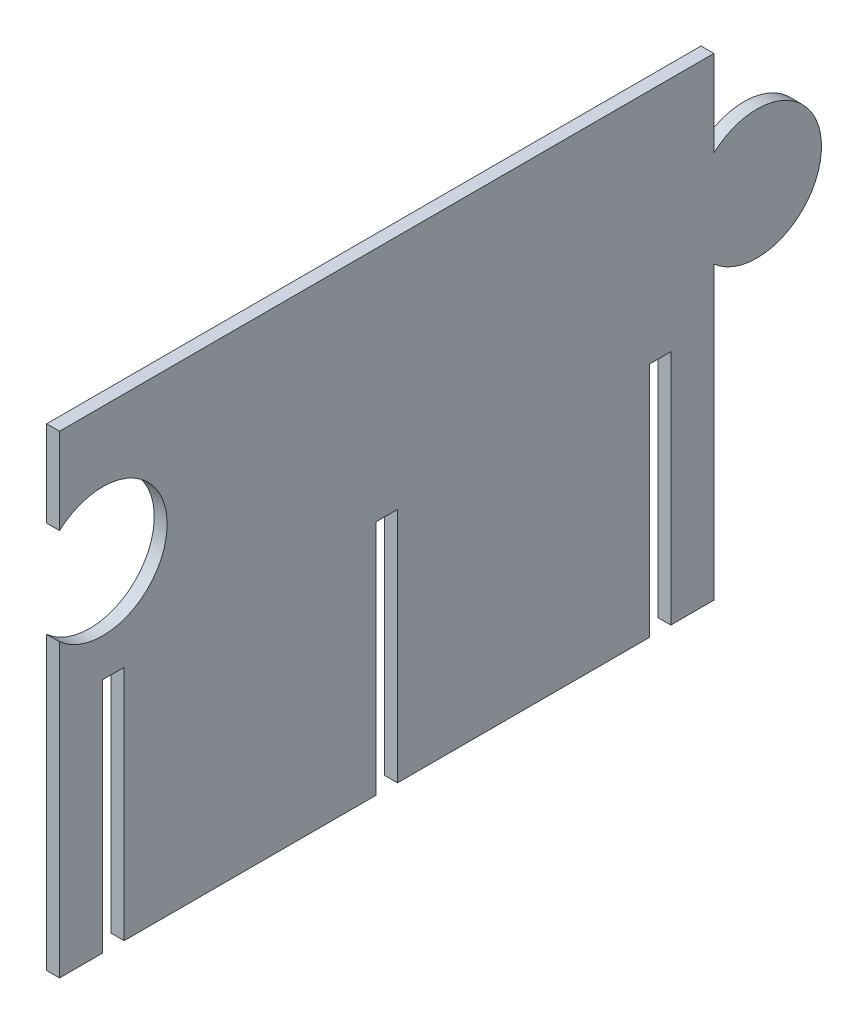
SolidWorks part; units mm, degrees
ref_plane "Plan de face" through (0, 0, 0) normal (0, 0, 1) x (1, 0, 0)
ref_plane "Plan de dessus" through (0, 0, 0) normal (0, 1, 0) x (1, 0, 0)
ref_plane "Plan de droite" through (0, 0, 0) normal (1, 0, 0) x (0, 0, -1)
sketch "Esquisse2" plane through (0, 0, -25.3208) normal (1, 0, 0) x (0, 0, -1)
  line L0 (-45.3299, 87.1104) -> (-45.3299, 67.1104)
  line L1 (-45.3299, -22.8896) -> (-35.3299, -22.8896)
  line L2 (-35.3299, -22.8896) -> (-35.3299, 32.1104)
  line L3 (-35.3299, 32.1104) -> (-30.3299, 32.1104)
  line L4 (-30.3299, 32.1104) -> (-30.3299, -22.8896)
  line L5 (-30.3299, -22.8896) -> (28.1701, -22.8896)
  line L6 (28.1701, -22.8896) -> (28.1701, 32.1104)
  line L7 (28.1701, 32.1104) -> (33.1701, 32.1104)
  line L8 (33.1701, 32.1104) -> (33.1701, -22.8896)
  line L9 (33.1701, -22.8896) -> (91.6701, -22.8896)
  line L10 (91.6701, -22.8896) -> (91.6701, 32.1104)
  line L11 (91.6701, 32.1104) -> (96.6701, 32.1104)
  line L12 (96.6701, 32.1104) -> (96.6701, -22.8896)
  line L13 (96.6701, -22.8896) -> (106.6701, -22.8896)
  line L14 (106.6701, 87.1104) -> (106.6701, 67.1104)
  line L15 (106.6701, 87.1104) -> (-45.3299, 87.1104)
  line L16 (-45.3299, 44.7497) -> (-45.3299, -22.8896)
  line L17 (106.6701, 44.7497) -> (106.6701, -22.8896)
  arc A0 (106.6701, 67.1104) -> (106.6701, 44.7497) centre (116.6701, 55.93) cw
  arc A1 (-45.3299, 67.1104) -> (-45.3299, 44.7497) centre (-35.3299, 55.93) cw
  point P27 (131.6701, 55.93)
  dimension "D16" = 15
  dimension "D1" = 10
  dimension "D3" = 152
  dimension "D4" = 58.5
  dimension "D5" = 10
  dimension "D6" = 5
  dimension "D7" = 5
  dimension "D8" = 5
  dimension "D9" = 58.5
  dimension "D10" = 110
  dimension "D11" = 20
  dimension "D12" = 67.6393
  dimension "D13" = 110
  dimension "D14" = 20
  dimension "D15" = 110
  dimension "D17" = 15
  dimension "D19" = 55
  dimension "D20" = 10
  dimension "D21" = 10
  dimension "D22" = 55
  dimension "D23" = 110
extrude "Boss.-Extru.1" add sketch "Esquisse2" along normal blind 3 contours L17 L13 L12 L11 L10 L9 L8 L7 L6 L5 L4 L3 L2 L1 L16 A1 L0 L15 L14 A0
